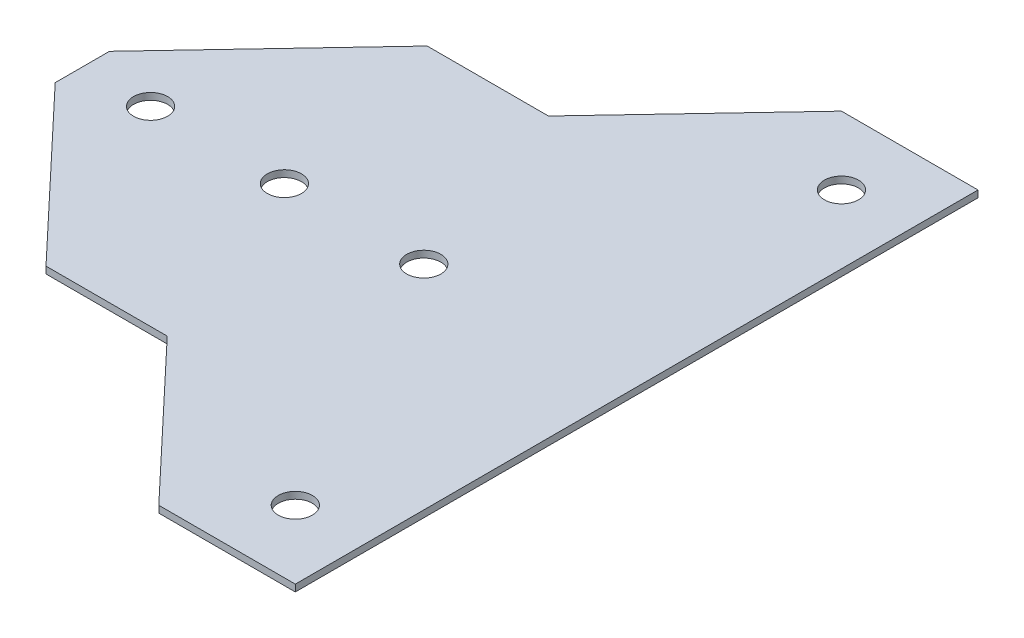
SolidWorks part; units mm, degrees
material "ABS"
ref_plane "Front Plane" through (0, 0, 0) normal (0, 0, 1) x (1, 0, 0)
ref_plane "Top Plane" through (0, 0, 0) normal (0, 1, 0) x (1, 0, 0)
ref_plane "Right Plane" through (0, 0, 0) normal (1, 0, 0) x (0, 0, -1)
sketch "Sketch1" plane through (0, 0, 0) normal (0, 1, 0) x (1, 0, 0)
  line L9 (30.6, 0) -> (-30.6, 0) construction
  line L10 (20.6, 50) -> (40.6, 50)
  line L11 (-40.6, 3.9738) -> (-40.6, -3.9738)
  line L12 (20.6, -50) -> (40.6, -50)
  line L13 (40.6, 50) -> (40.6, -50)
  line L14 (30.6, -40) -> (40.6, -40) construction
  line L15 (30.6, -50) -> (30.6, -40) construction
  line L17 (30.6, 40) -> (30.6, -40) construction
  line L20 (-18, 19.52) -> (12, 19.52) construction
  line L21 (-18, 27.92) -> (16.42, 27.92) construction
  line L22 (-18, 27.92) -> (-18, 19.52) construction
  line L23 (-18, -5.5) -> (16.42, -5.5) construction
  line L24 (16.42, 27.92) -> (16.42, -5.5) construction
  line L25 (-0.79, -5.5) -> (-0.79, 14.52) construction
  line L26 (12, 19.52) -> (12, 14.52) construction
  line L27 (12, 14.52) -> (-18, 14.52) construction
  line L28 (-18, 14.52) -> (-18, -5.5) construction
  line L29 (0, 27.92) -> (0, 0) construction
  line L30 (-40.6, 0) -> (-30.6, 0) construction
  line L31 (-30.6, 0) -> (-37.8725, -6.8637) construction
  line L32 (20.6, 50) -> (-0.2387, 27.92)
  line L33 (-0.2387, 27.92) -> (-18, 27.92)
  line L34 (-18, 27.92) -> (-40.6, 3.9738)
  line L35 (-18, -27.92) -> (-40.6, -3.9738)
  line L36 (-0.2387, -27.92) -> (-18, -27.92)
  line L37 (20.6, -50) -> (-0.2387, -27.92)
  circle A4 centre (-30.6, 0) radius 2.5
  circle A5 centre (30.6, 40) radius 2.5
  circle A6 centre (30.6, -40) radius 2.5
  circle A7 centre (9.42, 0) radius 2.5
  circle A8 centre (-11, 0) radius 2.5
  point P0 (0, 0)
  point P7 (-2.4974, -27.92)
  point P14 (32.5257, -50)
  point P16 (30.6, -50)
  point P19 (21.6831, -44.5264)
  point P25 (-36.348, -8.1829)
  point P26 (40.6, 50)
  point P31 (-18, -5.5)
  dimension "D7" = 34.42
  dimension "D3" = 10
  dimension "D5" = 5
  dimension "D14" = 5
  dimension "D4" = 80
  dimension "D6" = 61.2
  dimension "D8" = 33.42
  dimension "D9" = 30
  dimension "D10" = 8.4
  dimension "D11" = 5
  dimension "D12" = 5.5
  dimension "D13" = 7
  dimension "D15" = 18
extrude "Boss-Extrude1" add sketch "Sketch1" along normal blind 1
